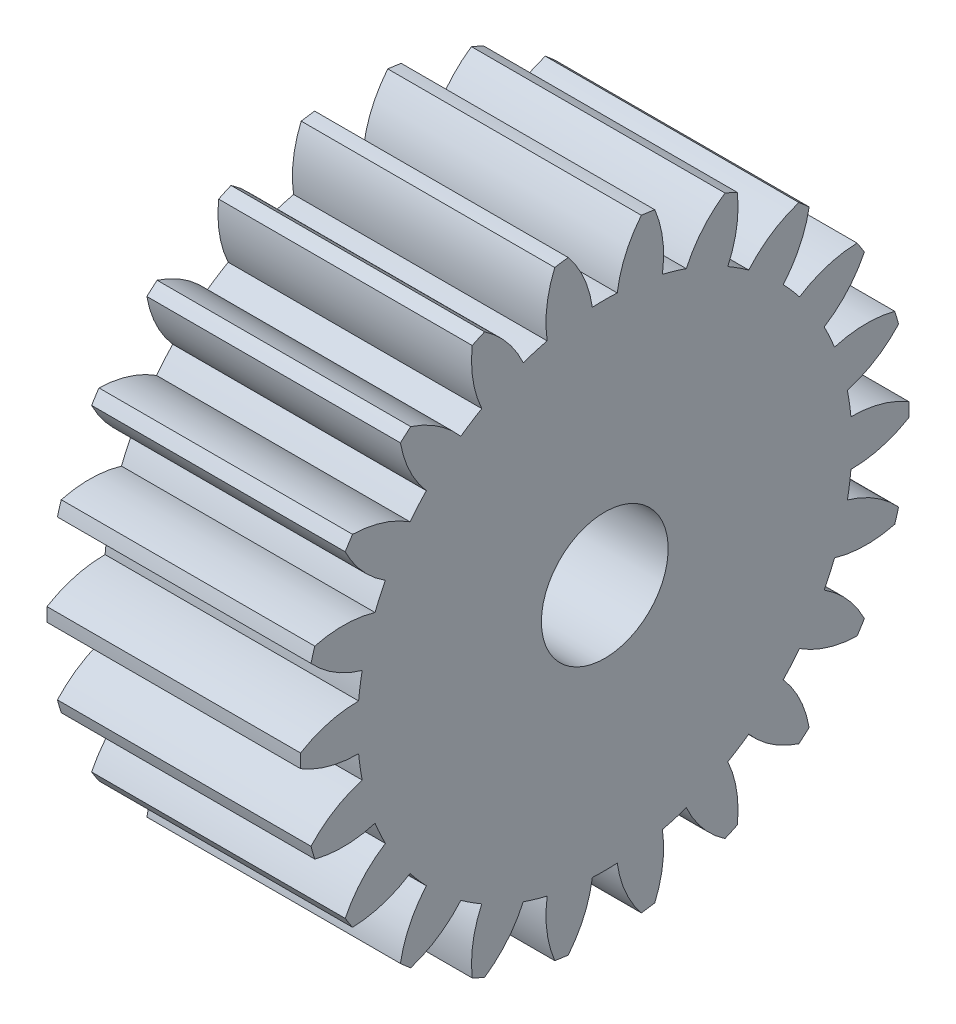
SolidWorks part; units mm, degrees
ref_plane "Plane1" through (0, 0, 0) normal (0, 0, 1) x (1, 0, 0)
ref_plane "Plane2" through (0, 0, 0) normal (0, 1, 0) x (1, 0, 0)
ref_plane "Plane3" through (0, 0, 0) normal (1, 0, 0) x (0, 0, -1)
other "Configuration Table"
sketch "HoldingSke" plane through (0, 0, 0) normal (0, 1, 0) x (1, 0, 0)
  line L0 (0, 0) -> (0.9272, -0.3746)
  line L1 (-15, 0) -> (100, 0) construction
  line L2 (0, 0) -> (-2.1039, 2.3779)
  line L3 (0, 0) -> (-11.863, 4.5341)
  line L4 (0, 0) -> (8.0072, 3.2351)
  line L5 (0, 0) -> (-46.8476, -17.4728)
  line L6 (0, 0) -> (-8.2896, -5.593)
  line L7 (-2.1039, 2.3779) -> (8.6586, 51.2059)
  line L8 (-76.2, 54.61) -> (-75.3, 54.61)
  line L9 (-71.009, 38.7566) -> (-53.1078, 45.2721)
  line L10 (-76.2, 71.12) -> (104.1128, 71.12)
  line L11 (0, 0) -> (-10, 0)
  line L12 (-76.2, 101.6) -> (-76.162, 101.6)
  line L13 (24.9733, 27.94) -> (52.9518, 28.4284)
  line L14 (24.9733, 27.94) -> (24.9743, 27.94)
  line L15 (24.9733, 27.94) -> (100.4006, 29.5858)
  line L16 (-63.627, -1) -> (-12.827, -1)
  circle A0 centre (0, 0) radius 2.5
  circle A1 centre (0, 0) radius 9.749
  circle A2 centre (0, 0) radius 37.5
  circle A3 centre (0, 0) radius 2.5
  dimension "MHD" = 19.498
  dimension "Hub_dia" = 75
  dimension "Bore" = 5
  dimension "MBD" = 5
  dimension "Num_teeth" = 22
  dimension "Pitch" = 1
  dimension "Overall_len" = 50
  dimension "Show_teeth" = 22
  dimension "Thickness" = 10
  dimension "OAL" = 50.0001
  dimension "T_dim" = 0.9
  dimension "Ap" = 20
  dimension "H" = 19.05
  dimension "Pitch_radius" = 180.3128
  dimension "Width" = 10
  dimension "Backlash" = 0.038
  dimension "Addendum_fac" = 1
  dimension "Dedendum_fac" = 1.25
  dimension "Clearance_fac" = 0.25
  dimension "Dedendum_add" = 0.001
  dimension "Module" = 1
sketch "BasProSke" plane through (0, 0, 0) normal (0, 1, 0) x (1, 0, 0)
  line L0 (-10, 0) -> (60, 0) construction
  line L1 (0, 0) -> (0, 12)
  line L2 (0, 0) -> (10, 0)
  line L3 (10, 0) -> (10, 12)
  line L4 (10, 12) -> (0, 12)
  dimension "Thickness" = 10
  dimension "Diameter" = 24
revolve "Base-Revolve" add sketch "BasProSke" angle 360 about L0
sketch "TooCutSke" plane through (0, 0, 0) normal (1, 0, 0) x (0, 0, -1)
  line L1 (0, 0) -> (0, 107) construction
  line L2 (0, 0) -> (-0.8512, 10.967) construction
  line L3 (0, 0) -> (-3.1242, 21.7296) construction
  line L4 (-0.8512, 10.967) -> (-1.5621, 10.8648) construction
  arc A0 (0.491, 9.7366) -> (-0.491, 9.7366) centre (0, 0) ccw
  arc A1 (1.4609, 11.9363) -> (-1.4609, 11.9363) centre (0, 0) ccw
  circle A2 centre (0, 0) radius 11 construction
  circle A3 centre (0, 0) radius 10.3366 construction
  arc A4 (-0.491, 9.7366) -> (-1.4609, 11.9363) centre (-4.8488, 9.1288) ccw
  arc A5 (1.4609, 11.9363) -> (0.491, 9.7366) centre (4.8488, 9.1288) ccw
  dimension "Root_dia" = 19.498
  dimension "Overcut_dia" = 24.0508
  dimension "Pitch_dia" = 22
  dimension "Base_dia" = 20.6732
  dimension "Flank_rad" = 4.4
  dimension "Half_ang" = 8.182
  dimension "Half_CT" = 0.7182
extrude "ToothCut" cut sketch "TooCutSke" along normal through all
fillet "Breaks" [suppressed] radius 0.02
fillet "RootFillets" [suppressed] radius 0.251
pattern_circular "TeethCuts" count 22 every 16.364 about axis through (-10, 0, 0) along (1, 0, 0) of "ToothCut", "RootFillets", "Breaks"
sketch "HubNeaOneSke" plane through (0, 0, 0) normal (-1, 0, 0) x (0, 0, 1)
  circle A0 centre (0, 0) radius 9.749
  dimension "Diameter" = 19.498
extrude "HubNearOne" [suppressed] add sketch "HubNeaOneSke" along normal blind 40.0001
sketch "HubNeaBotSke" plane through (0, 0, 0) normal (-1, 0, 0) x (0, 0, 1)
  circle A0 centre (0, 0) radius 9.749
  dimension "Diameter" = 19.498
extrude "HubNearBoth" [suppressed] add sketch "HubNeaBotSke" along normal blind 20
ref_plane "FarPln" through (10, 0, 0) normal (1, 0, 0) x (0, 0, -1)
sketch "HubFarSke" plane through (10, 0, 0) normal (1, 0, 0) x (0, 0, -1)
  circle A0 centre (0, 0) radius 9.749
  dimension "Diameter" = 19.498
extrude "HubFar" [suppressed] add sketch "HubFarSke" along normal blind 20
sketch "BorSke" plane through (0, 0, 0) normal (1, 0, 0) x (0, 0, -1)
  circle A0 centre (0, 0) radius 2.5
  dimension "Diameter" = 5
extrude "Bore" cut sketch "BorSke" along normal mid plane 100.0001
sketch "KeySke" plane through (0, 0, 0) normal (1, 0, 0) x (0, 0, -1)
  line L0 (-1, 0) -> (-1, 3.4)
  line L1 (-1, 3.4) -> (1, 3.4)
  line L2 (1, 3.4) -> (1, 0)
  line L3 (0, 0) -> (0, 34) construction
  line L4 (-1, 0) -> (1, 0)
  dimension "Offset" = 3.4
  dimension "Width" = 2
extrude "Keyway" [suppressed] cut sketch "KeySke" along normal mid plane 100.0001
pattern_circular "Keyway2" [suppressed] count 2 every 90 about axis through (-10, 0, 0) along (1, 0, 0)
equation "' \"Module@HoldingSke\" = 6.35"
equation "' \"Num_teeth@HoldingSke\" = 12"
equation "' \"Ap@HoldingSke\" =  20"
equation "' \"Ap@HoldingSke\" = 20"
equation "' \"Width@HoldingSke\" = 0.5 * 25.4"
equation "' \"Hub_dia@HoldingSke\"= 1 * 25.4"
equation "' \"Hub_dia@HoldingSke\" = 1 * 25.4"
equation "' \"Overall_len@HoldingSke\" = 1.0 * 25.4"
equation "' \"Bore@HoldingSke\" = 0.75 * 25.4"
equation "' \"T_dim@HoldingSke\" = 0.1 * 25.4"
equation "' \"Width@KeySke\" = 0.25 * 25.4"
equation "' \"Show_teeth@HoldingSke\" = 13"
equation "' \"Backlash@HoldingSke\" = 0.009 * 25.4"
equation "' \"Addendum_fac@HoldingSke\" = 1.0"
equation "' \"Dedendum_fac@HoldingSke\" = 1.25"
equation "' \"Dedendum_add@HoldingSke\" = 0.00005 * 25.4"
equation "' \"Clearance_fac@HoldingSke\" = 0.25"
equation "\"Pitch@HoldingSke\" = 1 / \"Module@HoldingSke\""
equation "\"Overcut_dia@TooCutSke\" = (\"Num_teeth@HoldingSke\" + 2 * \"Addendum_fac@HoldingSke\") / \"Pitch@HoldingSke\" + 0.002 * 25.4"
equation "\"Pitch_dia@TooCutSke\" = \"Num_teeth@HoldingSke\" / \"Pitch@HoldingSke\""
equation "\"Base_dia@TooCutSke\" = \"Num_teeth@HoldingSke\" / \"Pitch@HoldingSke\" * cos((\"Ap@HoldingSke\"  * 3.14159265 / 180))"
equation "\"Root_dia@TooCutSke\" = (\"Num_teeth@HoldingSke\" + 2) / \"Pitch@HoldingSke\" - 2 * (\"Addendum_fac@HoldingSke\" + \"Dedendum_fac@HoldingSke\") / \"Pitch@HoldingSke\" - \"Dedendum_add@HoldingSke\" * 2"
equation "\"Half_ang@TooCutSke\" = 180 / \"Num_teeth@HoldingSke\""
equation "\"Half_CT@TooCutSke\" = \"Num_teeth@HoldingSke\" / \"Pitch@HoldingSke\" * sin((3.14159265 / 2 / \"Num_teeth@HoldingSke\")) / 2 - 7 * \"Backlash@HoldingSke\" / 4"
equation "\"Flank_rad@TooCutSke\" = \"Num_teeth@HoldingSke\" / \"Pitch@HoldingSke\" / 5"
equation "\"Radius@RootFillets\" = \"Clearance_fac@HoldingSke\" / \"Pitch@HoldingSke\" + \"Dedendum_add@HoldingSke\""
equation "\"Break_rad@Breaks\" = 0.02 / \"Pitch@HoldingSke\""
equation "\"Thickness@HoldingSke\" = \"Width@HoldingSke\""
equation "\"OAL@HoldingSke\" = \"Thickness@HoldingSke\""
equation "\"MHD@HoldingSke\" = (\"Num_teeth@HoldingSke\" + 2) / \"Pitch@HoldingSke\" - 2 * (\"Addendum_fac@HoldingSke\" + \"Dedendum_fac@HoldingSke\")  / \"Pitch@HoldingSke\" - \"Dedendum_add@HoldingSke\" * 2"
equation "\"MBD@HoldingSke\" = (\"Num_teeth@HoldingSke\" + 2) / \"Pitch@HoldingSke\" - 2 * (\"Addendum_fac@HoldingSke\" + \"Dedendum_fac@HoldingSke\")  / \"Pitch@HoldingSke\" - \"Dedendum_add@HoldingSke\" * 2 - 0.002 * 25.4"
equation "\"MHD@HoldingSke\" = ((sgn( \"MHD@HoldingSke\" - \"Hub_dia@HoldingSke\" )-1)*( \"MHD@HoldingSke\" - \"Hub_dia@HoldingSke\" ))/-2+ \"Hub_dia@HoldingSke\""
equation "\"MBD@HoldingSke\" = ((sgn( \"MBD@HoldingSke\" - \"Bore@HoldingSke\" )-1)*( \"MBD@HoldingSke\" - \"Bore@HoldingSke\" ))/-2+ \"Bore@HoldingSke\""
equation "\"OAL@HoldingSke\" = ((sgn( \"OAL@HoldingSke\" - \"Overall_len@HoldingSke\" )+1)*( \"OAL@HoldingSke\" - \"Overall_len@HoldingSke\" ))/2 + \"Overall_len@HoldingSke\" + 0.000002 * 25.4"
equation "\"Num_teeth@TeethCuts\" = int( \"Show_teeth@HoldingSke\" ) + 1"
equation "\"Num_teeth@TeethCuts\" = ((sgn( \"Num_teeth@TeethCuts\" - \"Num_teeth@HoldingSke\" )-1)*( \"Num_teeth@TeethCuts\" - \"Num_teeth@HoldingSke\" ))/-2+ \"Num_teeth@HoldingSke\""
equation "\"Num_teeth@TeethCuts\" = ((sgn( \"Num_teeth@TeethCuts\" - 2.0)+1)*( \"Num_teeth@TeethCuts\" - 2.0))/2 +2.0"
equation "\"Angle@TeethCuts\" = 360.0 / \"Num_teeth@HoldingSke\""
equation "\"Diameter@BasProSke\" = (\"Num_teeth@HoldingSke\" + 2 * \"Addendum_fac@HoldingSke\") / \"Pitch@HoldingSke\""
equation "\"Thickness@BasProSke\"  = \"Thickness@HoldingSke\""
equation "' \"Fillet_rad@BasProSke\" =  \"Thickness@HoldingSke\" * 0.05"
equation "' \"Fillet_rad@BasProSke\" = \"Thickness@HoldingSke\" * 0.05"
equation "\"MHD@HoldingSke\" = ((sgn( \"MHD@HoldingSke\" - \"Root_dia@TooCutSke\" )-1)*( \"MHD@HoldingSke\" - \"Root_dia@TooCutSke\" ))/-2+ \"Root_dia@TooCutSke\""
equation "\"Diameter@HubNeaOneSke\" = \"MHD@HoldingSke\""
equation "\"Length@HubNearOne\" = \"OAL@HoldingSke\" - \"Thickness@BasProSke\""
equation "\"Diameter@HubNeaBotSke\" = \"MHD@HoldingSke\""
equation "\"Length@HubNearBoth\" = ( \"OAL@HoldingSke\" - \"Thickness@BasProSke\" ) / 2.0"
equation "\"Thickness@FarPln\" = \"Thickness@BasProSke\""
equation "\"Diameter@HubFarSke\" = \"MHD@HoldingSke\""
equation "\"Length@HubFar\" = ( \"OAL@HoldingSke\" - \"Thickness@BasProSke\" ) / 2.0"
equation "\"Diameter@BorSke\" = \"MBD@HoldingSke\""
equation "\"D1@Bore\" = \"OAL@HoldingSke\" * 2.0"
equation "\"D1@Keyway\" = \"OAL@HoldingSke\" * 2.0"
equation "\"Offset@KeySke\" = \"T_dim@HoldingSke\" + \"MBD@HoldingSke\" / 2.0"
